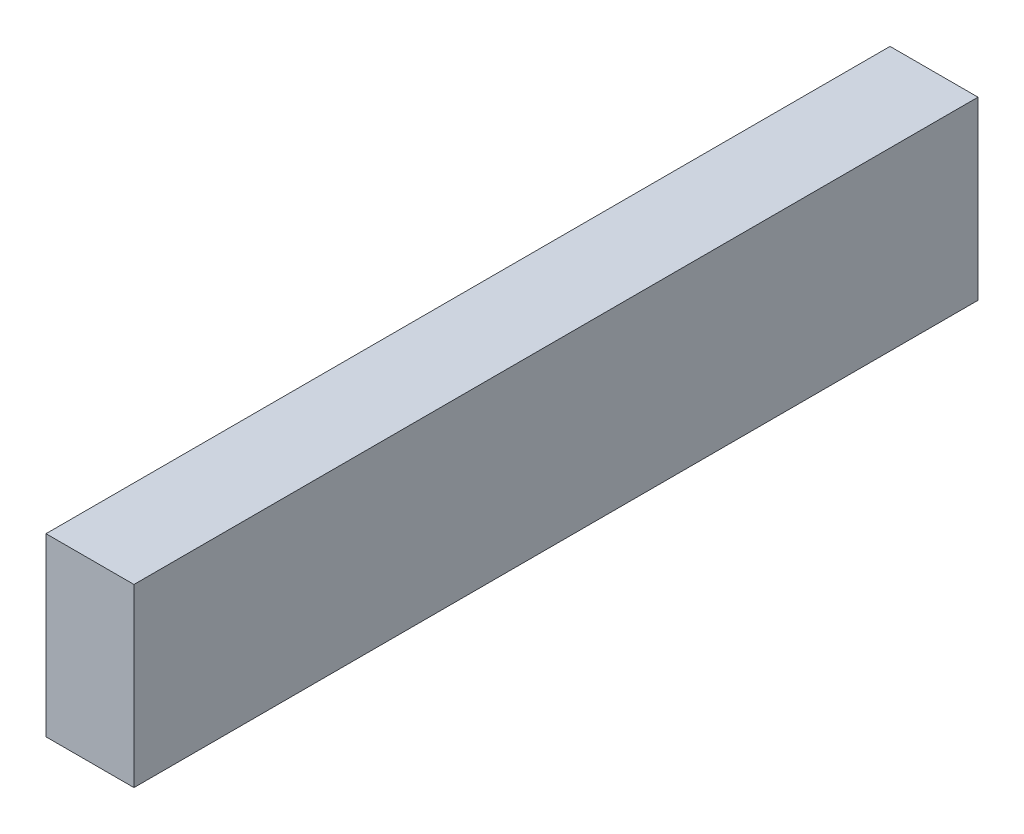
SolidWorks part; units mm, degrees
material "Cedar"
ref_plane "Front Plane" through (0, 0, 0) normal (0, 0, 1) x (1, 0, 0)
ref_plane "Top Plane" through (0, 0, 0) normal (0, 1, 0) x (1, 0, 0)
ref_plane "Right Plane" through (0, 0, 0) normal (1, 0, 0) x (0, 0, -1)
sketch "Sketch1" plane through (0, 0, 0) normal (1, 0, 0) x (0, 0, -1)
  line L1 (-39.7099, 28.2346) -> (143.0685, 28.2346)
  line L2 (-39.7099, 28.2346) -> (-39.7099, -9.8654)
  line L3 (-39.7099, -9.8654) -> (143.0685, -9.8654)
  line L4 (143.0685, 28.2346) -> (143.0685, -9.8654)
  dimension "D1" = 182.7784
  dimension "D2" = 38.1
extrude "Boss-Extrude1" add sketch "Sketch1" along normal blind 19.05
